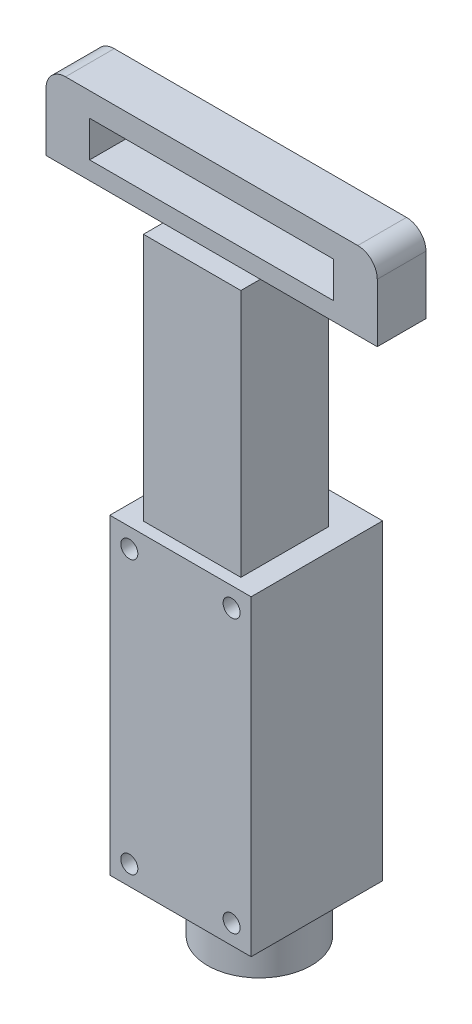
SolidWorks part; units mm, degrees
ref_plane "前视基准面" through (0, 0, 0) normal (0, 0, 1) x (1, 0, 0)
ref_plane "上视基准面" through (0, 0, 0) normal (0, 1, 0) x (1, 0, 0)
ref_plane "右视基准面" through (0, 0, 0) normal (1, 0, 0) x (0, 0, -1)
ref_plane "基准面4" through (0, 0, 13.5) normal (0, 0, 1) x (1, 0, 0)
sketch "草图1" plane through (0, 0, 13.5) normal (0, 0, 1) x (1, 0, 0)
  line L0 (14.5, -32) -> (14.5, 32)
  line L1 (14.5, 32) -> (-14.5, 32)
  line L2 (-14.5, 32) -> (-14.5, -32)
  line L3 (-14.5, -32) -> (14.5, -32)
extrude "凸台-拉伸1" add sketch "草图1" against normal blind 27
sketch "草图2" plane through (0, 32, 0) normal (0, 1, 0) x (-1, 0, 0)
  line L0 (-10, -6.9) -> (-10, 11.1)
  line L1 (-10, 11.1) -> (10, 11.1)
  line L2 (10, 11.1) -> (10, -6.9)
  line L3 (10, -6.9) -> (-10, -6.9)
extrude "凸台-拉伸2" add sketch "草图2" along normal blind 51
sketch "草图3" plane through (0, 83, 0) normal (0, 1, 0) x (-1, 0, 0)
  line L0 (-10, 7.1) -> (34, 7.1)
  line L1 (34, 7.1) -> (34, -2.9)
  line L2 (34, -2.9) -> (-10, -2.9)
  line L3 (-10, -2.9) -> (-10, 7.1)
extrude "凸台-拉伸3" add sketch "草图3" along normal blind 16
sketch "草图4" plane through (10, 0, 0) normal (1, 0, 0) x (0, 0, -1)
  line L0 (2.9, 99) -> (2.9, 83)
  line L1 (2.9, 83) -> (-7.1, 83)
  line L2 (-7.1, 83) -> (-7.1, 99)
  line L3 (-7.1, 99) -> (2.9, 99)
extrude "凸台-拉伸4" add sketch "草图4" along normal blind 24
sketch "草图5" plane through (0, 0, 7.1) normal (0, 0, 1) x (1, 0, 0)
  line L0 (-25.05, 86.7) -> (25.05, 86.7)
  line L1 (25.05, 86.7) -> (25.05, 94.1)
  line L2 (25.05, 94.1) -> (-25.05, 94.1)
  line L3 (-25.05, 94.1) -> (-25.05, 86.7)
extrude "切除-拉伸1" cut sketch "草图5" against normal through all
ref_plane "基准面5" through (0, 0, -2.7) normal (0, 0, 1) x (1, 0, 0)
sketch "草图6" plane through (0, 0, -2.7) normal (0, 0, 1) x (1, 0, 0)
  line L0 (10.65, -32) -> (0, -32)
  line L1 (0, -32) -> (0, -43.6)
  line L2 (0, -43.6) -> (10.65, -43.6)
  line L3 (10.65, -43.6) -> (10.65, -32)
  line L4 (0, -32) -> (0, -43.6) construction
revolve "旋转1" add sketch "草图6" angle 360 about L4
hole_wizard "Ø3.5 (3.5) 直径孔1" positions "草图8" profile "草图7" hole size "Ø3.5" standard "ANSI Metric"
sketch "草图8" plane through (0, 0, 13.5) normal (0, 0, 1) x (1, 0, 0)
  point P0 (-10.5, -28)
  point P1 (10.5, -28)
  point P2 (-10.5, 28)
  point P3 (10.5, 28)
sketch "草图7" plane through (-10.5, -28, 13.5) normal (1, 0, 0) x (0, -1, 0)
  line L0 (0, 0) -> (0, 27)
  line L1 (0, 27) -> (1.75, 27)
  line L2 (1.75, 27) -> (1.75, 0)
  line L5 (1.75, 0) -> (0, 0)
  line L11 (0, -6.35) -> (0, 107.95) construction
  dimension "通孔孔直径" = 3.5
  dimension "通孔孔深度" = 27
fillet "圆角1" radius 4 2 edges at (-34, 99, 2.1) (34, 99, 2.1)
